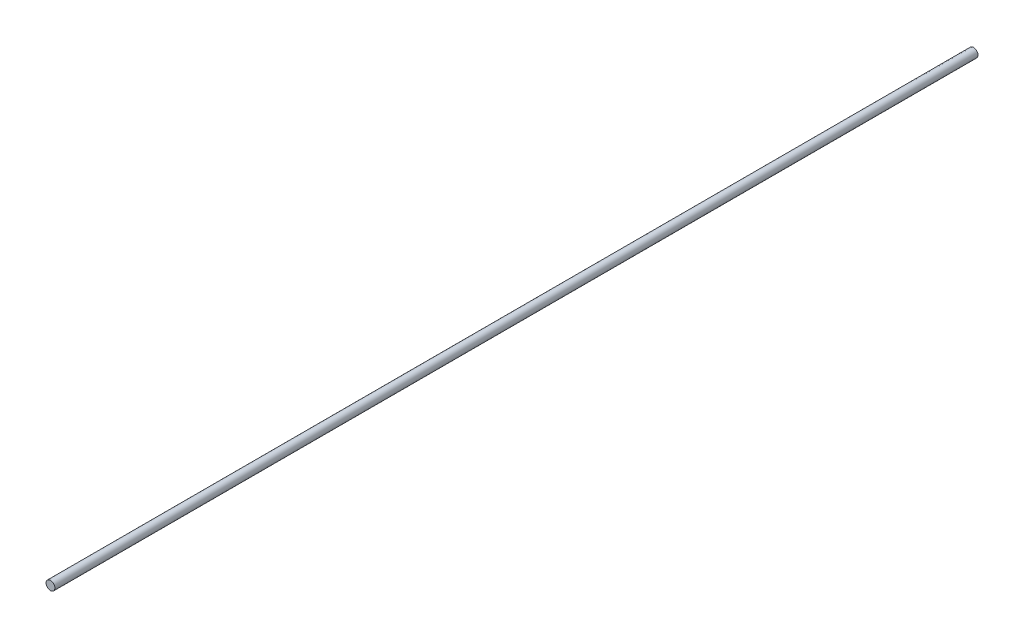
SolidWorks part; units mm, degrees
ref_plane "Front Plane" through (0, 0, 0) normal (0, 0, 1) x (1, 0, 0)
ref_plane "Top Plane" through (0, 0, 0) normal (0, 1, 0) x (1, 0, 0)
ref_plane "Right Plane" through (0, 0, 0) normal (1, 0, 0) x (0, 0, -1)
sketch "Sketch1" plane through (0, 0, 0) normal (0, 0, 1) x (1, 0, 0)
  circle A0 centre (86.9962, -86.9962) radius 3.5 construction
  circle A1 centre (86.9962, -86.9962) radius 3.5
extrude "Boss-Extrude1" add sketch "Sketch1" along normal offset from surface 25.4 and the other way offset from surface (72.094 mm away) 25.4 contours A1
